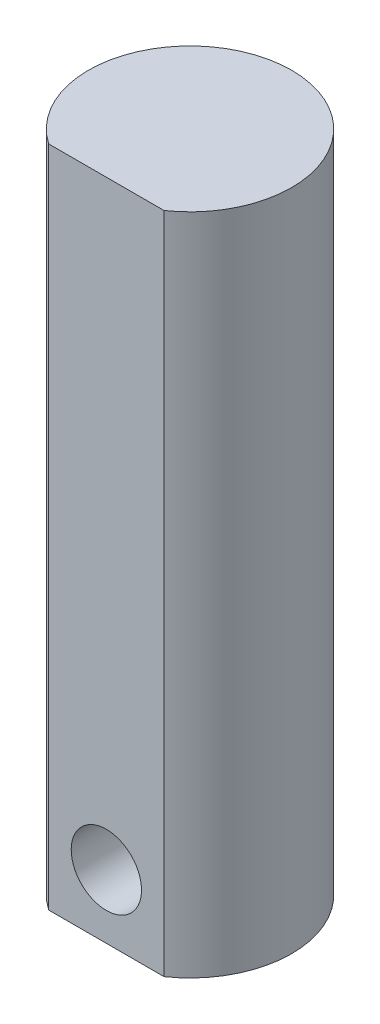
SolidWorks part; units mm, degrees
ref_plane "Plan de face" through (0, 0, 0) normal (0, 0, 1) x (1, 0, 0)
ref_plane "Plan de dessus" through (0, 0, 0) normal (0, 1, 0) x (1, 0, 0)
ref_plane "Plan de droite" through (0, 0, 0) normal (1, 0, 0) x (0, 0, -1)
sketch "Esquisse2" plane through (0, 0, 0) normal (0, 1, 0) x (1, 0, 0)
  line L0 (-4.1, -5.949) -> (4.1, -5.949)
  circle A0 centre (0, 0) radius 7.225 construction
  arc A1 (-4.1, -5.949) -> (4.1, -5.949) centre (0, 0) cw
  dimension "D1" = 14.45
  dimension "D2" = 8.2
extrude "Boss.-Extru.1" add sketch "Esquisse2" along normal mid plane 47.17 contours A1 L0
sketch "Esquisse4" plane through (0, 0, 0) normal (0, 0, 1) x (1, 0, 0)
  line L8 (-114.1, -133.585) -> (114.1, -133.585)
  line L9 (114.1, -133.585) -> (114.1, 133.585)
  line L10 (114.1, 133.585) -> (-114.1, 133.585)
  line L11 (-114.1, 133.585) -> (-114.1, -133.585)
  line L12 (-114.1, -133.585) -> (114.1, -133.585)
  line L13 (114.1, -133.585) -> (114.1, 133.585)
  line L14 (114.1, 133.585) -> (-114.1, 133.585)
  line L15 (-114.1, 133.585) -> (-114.1, -133.585)
  circle A4 centre (0, -19.06) radius 2.5
  dimension "D2" = 110
  dimension "D4" = 5
extrude "Enlèv. mat.-Extru.5" cut sketch "Esquisse4" against normal blind 3.75 from surface at 5.949 flip side to cut starting at face at (0, 0, 5.949)
